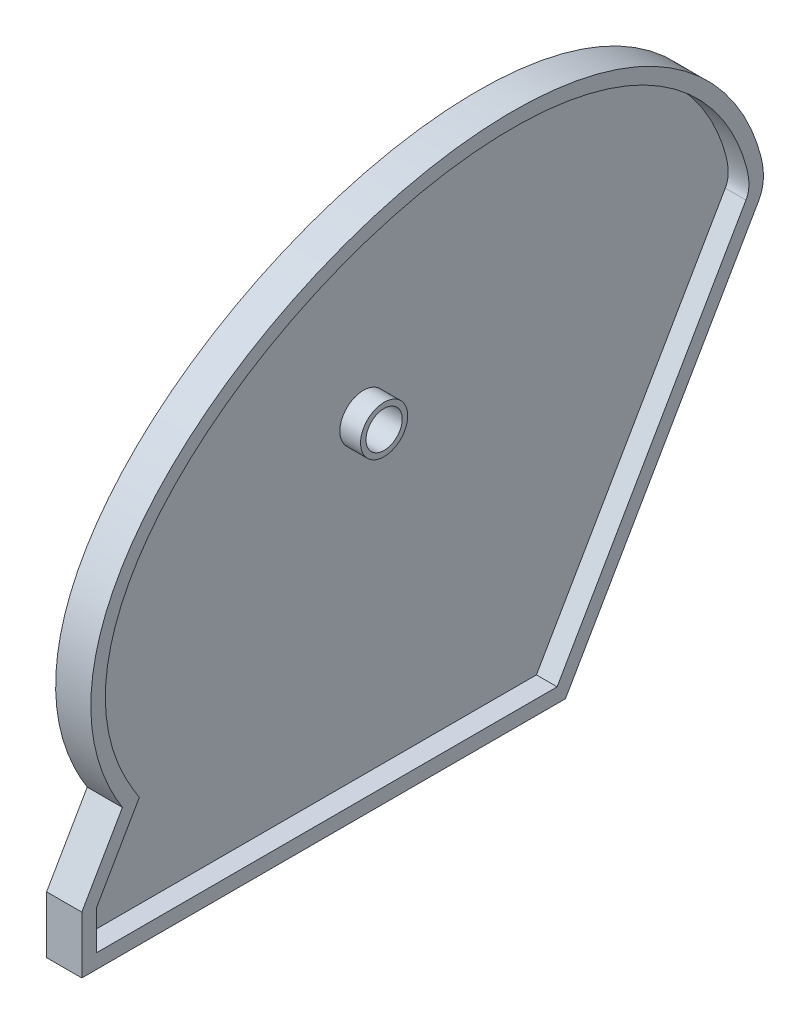
SolidWorks part; units mm, degrees
ref_plane "Front Plane" through (0, 0, 0) normal (0, 0, 1) x (1, 0, 0)
ref_plane "Top Plane" through (0, 0, 0) normal (0, 1, 0) x (1, 0, 0)
ref_plane "Right Plane" through (0, 0, 0) normal (1, 0, 0) x (0, 0, -1)
sketch "Sketch1" plane through (0, 0, 0) normal (1, 0, 0) x (0, 0, -1)
  line L0 (0, 0) -> (-67.7418, 0)
  line L1 (0, 0) -> (27.0383, 46.8317)
  line L2 (-67.7418, 0) -> (-67.7418, 7.9904)
  line L3 (-67.7418, 7.9904) -> (-62.0527, 17.8441)
  line L4 (0, 0) -> (0, 45.3644) construction
  line L5 (0, 45.3644) -> (-25.4, 45.3644) construction
  circle A0 centre (-25.4, 45.3644) radius 1.27
  spline S0 degree 3 poles (-62.0527, 17.8441) (-83.5205, 52.1817) (-7.1969, 94.4521) (26.0937, 59.7977) (28.1532, 48.7627) (27.0383, 46.8317) knots 0 0 0 0 0.772335 0.951961 1 1 1 1
  point P7 (-67.7418, 7.9904)
  point P10 (-25.4, 45.3644)
  dimension "D7" = 2.54
  dimension "D1" = 120
  dimension "D2" = 67.7418
  dimension "D3" = 54.0766
  dimension "D4" = 60
  dimension "D5" = 45.3644
  dimension "D6" = 25.4
extrude "Boss-Extrude1" add sketch "Sketch1" along normal blind 4.9276
shell "Shell1" thickness 2.032
hole_wizard "CSK for #0 Flat Head Machine Screw (100)2" positions "Sketch6" profile "Sketch7" countersink size "#0" standard "ANSI Inch" end condition through all
sketch "Sketch6" plane through (0, 0, 0) normal (-1, 0, 0) x (0, 0, 1)
  point P0 (25.4, 45.3644)
sketch "Sketch7" plane through (0, 45.3644, 25.4) normal (0, 1, 0) x (0, 0, 1)
  line L0 (0, 0) -> (0, 4.9276)
  line L1 (0, 4.9276) -> (2.54, 4.9276)
  line L2 (2.54, 4.9276) -> (2.54, 1.0657)
  line L3 (2.54, 1.0657) -> (3.81, 0)
  line L5 (3.81, 0) -> (0, 0)
  line L6 (-2.54, 1.0657) -> (-3.81, 0) construction
  line L11 (0, -6.35) -> (0, 107.95) construction
  dimension "Thru Hole Dia." = 5.08
  dimension "Thru Hole Depth" = 4.9276
  dimension "Near C'Sink Dia." = 7.62
  dimension "Near C'Sink Angle" = 100
